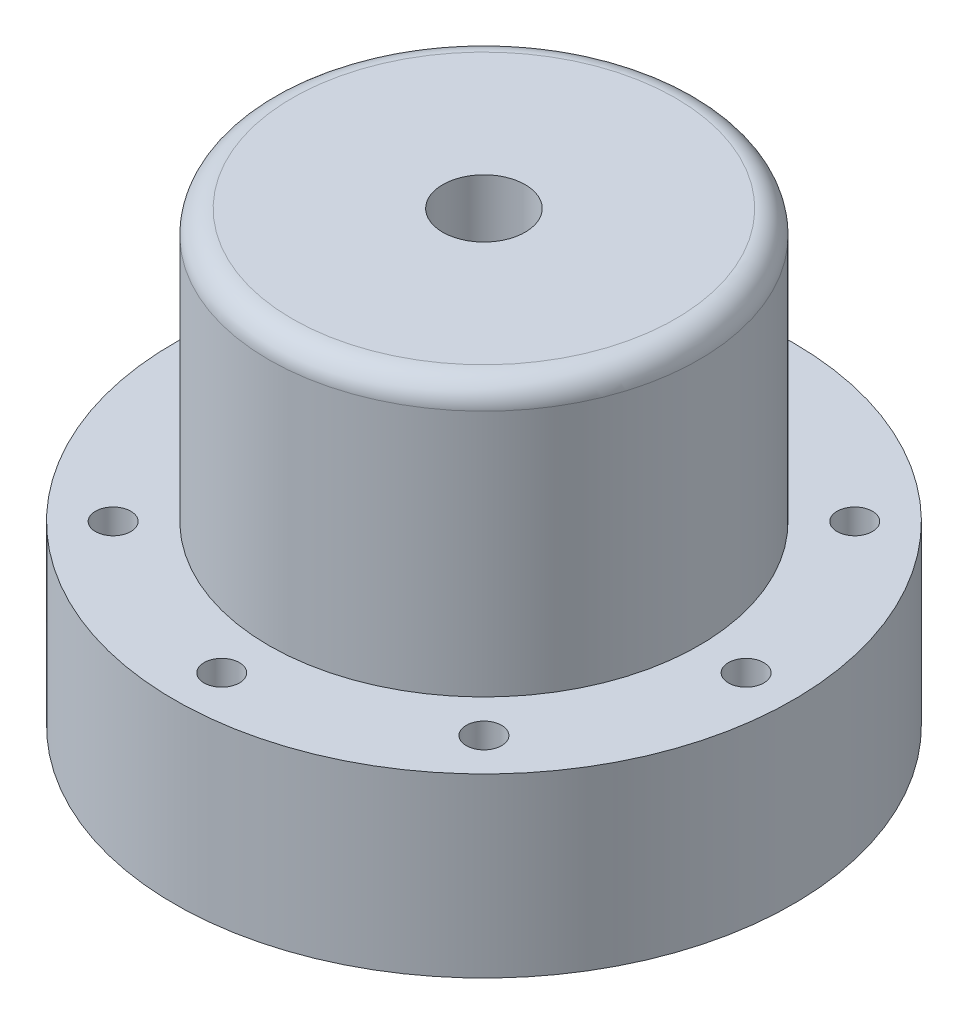
SolidWorks part; units mm, degrees
ref_plane "Front Plane" through (0, 0, 0) normal (0, 0, 1) x (1, 0, 0)
ref_plane "Top Plane" through (0, 0, 0) normal (0, 1, 0) x (1, 0, 0)
ref_plane "Right Plane" through (0, 0, 0) normal (1, 0, 0) x (0, 0, -1)
sketch "Sketch1" plane through (0, 0, 0) normal (0, 1, 0) x (1, 0, 0)
  circle A0 centre (0, 0) radius 18.25
  circle A1 centre (0, 0) radius 13.25
  dimension "D1" = 26.5
  dimension "D2" = 5
extrude "Boss-Extrude1" add sketch "Sketch1" along normal blind 18
sketch "Sketch2" plane through (0, 0, 0) normal (0, -1, 0) x (1, 0, 0)
  circle A0 centre (0, 0) radius 26.25
  circle A1 centre (0, 0) radius 18.25 construction
  circle A2 centre (0, 0) radius 13.25
  circle A3 centre (0, 0) radius 13.25 construction
  dimension "D1" = 8
extrude "flange" add sketch "Sketch2" along normal blind 5
sketch "Sketch4" plane through (0, 0, 0) normal (0, 1, 0) x (1, 0, 0)
  line L0 (0, -22.25) -> (0, 0) construction
  line L1 (0, -22.25) -> (0, -26.25) construction
  line L2 (0, -26.25) -> (-12.1281, -26.25) construction
  line L3 (0, -18.25) -> (-3.6798, -18.25) construction
  line L4 (0, -22.25) -> (-5.4235, -22.25) construction
  line L5 (0, -18.25) -> (0, -22.25)
  circle A0 centre (0, -22.25) radius 1.5
  circle A1 centre (0, 0) radius 26.25 construction
  circle A2 centre (0, 0) radius 18.25 construction
  dimension "D1" = 3
extrude "Cut-Extrude1" cut sketch "Sketch4" against normal up to next
pattern_circular "CirPattern1" count 8 over 360 about axis through (0, 0, 0) along (0, 1, 0) of "Cut-Extrude1"
sketch "Sketch6" plane through (0, 18, 0) normal (0, 1, 0) x (1, 0, 0)
  circle A0 centre (0, 0) radius 18.25
  circle A1 centre (0, 0) radius 3.5
  circle A2 centre (0, 0) radius 18.25 construction
  dimension "D1" = 7
extrude "top" add sketch "Sketch6" along normal blind 5
sketch "Sketch7" plane through (0, -5, 0) normal (0, -1, 0) x (1, 0, 0)
  circle A0 centre (0, 0) radius 26.25
  circle A1 centre (0, 0) radius 18.25
  circle A2 centre (0, 0) radius 18.25
  circle A3 centre (0, 0) radius 26.25 construction
  circle A4 centre (0, 0) radius 19.25
  circle M3 centre (-22.25, 0) radius 1.5
  circle M4 centre (-15.7331, -15.7331) radius 1.5
  circle M5 centre (0, -22.25) radius 1.5
  circle M6 centre (15.7331, -15.7331) radius 1.5
  circle M7 centre (22.25, 0) radius 1.5
  circle M8 centre (15.7331, 15.7331) radius 1.5
  circle M9 centre (-15.7331, 15.7331) radius 1.5
  circle M10 centre (0, 22.25) radius 1.5
  circle M11 centre (0, 0) radius 26.25
  dimension "D2" = 1
  dimension "D1" = 0
extrude "Boss-Extrude5" add sketch "Sketch7" along normal blind 10 contours A4 M11 M4 M6 M8 M10 M9 M7 M5 M3
fillet "Fillet1" radius 2 1 edges at (0, 23, 18.25)
